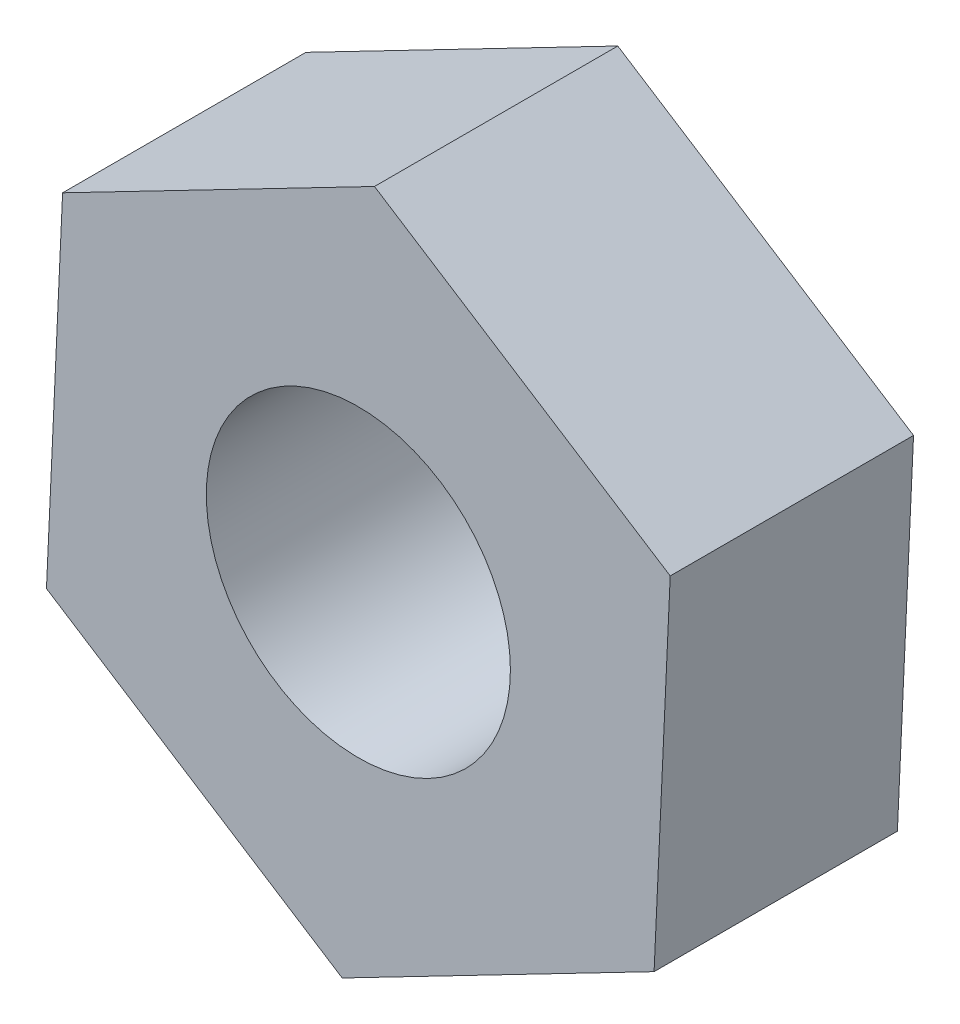
SolidWorks part; units mm, degrees
ref_plane "正面" through (0, 0, 0) normal (0, 0, 1) x (1, 0, 0)
ref_plane "平面" through (0, 0, 0) normal (0, 1, 0) x (1, 0, 0)
ref_plane "右側面" through (0, 0, 0) normal (1, 0, 0) x (0, 0, -1)
sketch "ｽｹｯﾁ1" plane through (0, 0, 0) normal (0, 0, 1) x (1, 0, 0)
  line L1 (-2.0509, -1.0616) -> (-0.1061, -2.307)
  line L2 (-0.1061, -2.307) -> (1.9448, -1.2454)
  line L3 (1.9448, -1.2454) -> (2.0509, 1.0616)
  line L4 (2.0509, 1.0616) -> (0.1061, 2.307)
  line L5 (0.1061, 2.307) -> (-1.9448, 1.2454)
  line L6 (-1.9448, 1.2454) -> (-2.0509, -1.0616)
  circle A0 centre (0, 0) radius 2 construction
  circle A1 centre (0, 0) radius 1
  dimension "D2" = 2
  dimension "D1" = 4
extrude "ﾎﾞｽ - 押し出し1" add sketch "ｽｹｯﾁ1" along normal blind 1.6
